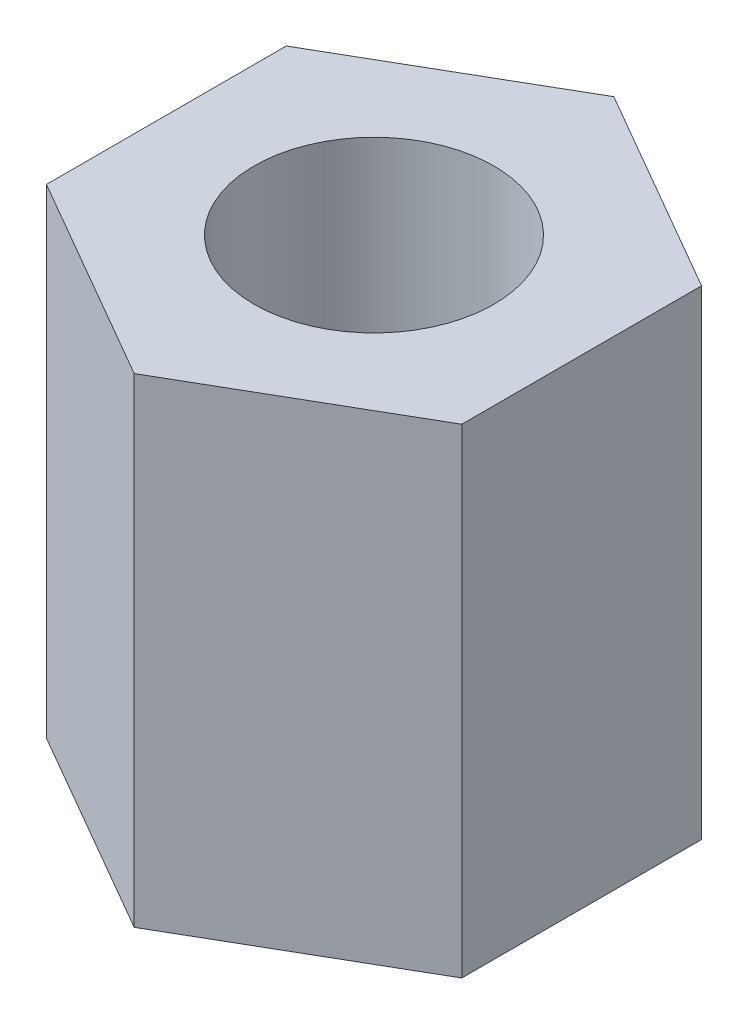
SolidWorks part; units mm, degrees
ref_plane "Face" through (0, 0, 0) normal (0, 0, 1) x (1, 0, 0)
ref_plane "Dessus" through (0, 0, 0) normal (0, 1, 0) x (1, 0, 0)
ref_plane "Droite" through (0, 0, 0) normal (1, 0, 0) x (0, 0, -1)
sketch "Esquisse1" plane through (0, 0, 0) normal (0, 1, 0) x (1, 0, 0)
  line L0 (0, 0) -> (0, 5.5688) construction
  line L1 (0, 5) -> (-4.3301, 2.5)
  line L2 (-4.3301, 2.5) -> (-4.3301, -2.5)
  line L3 (-4.3301, -2.5) -> (0, -5)
  line L4 (0, -5) -> (4.3301, -2.5)
  line L5 (4.3301, -2.5) -> (4.3301, 2.5)
  line L6 (4.3301, 2.5) -> (0, 5)
  circle A0 centre (0, 0) radius 4.3301 construction
  circle A1 centre (0, 0) radius 2.5
  dimension "D1" = 10
  dimension "D2" = 5
extrude "Extrusion1" add sketch "Esquisse1" along normal blind 10
